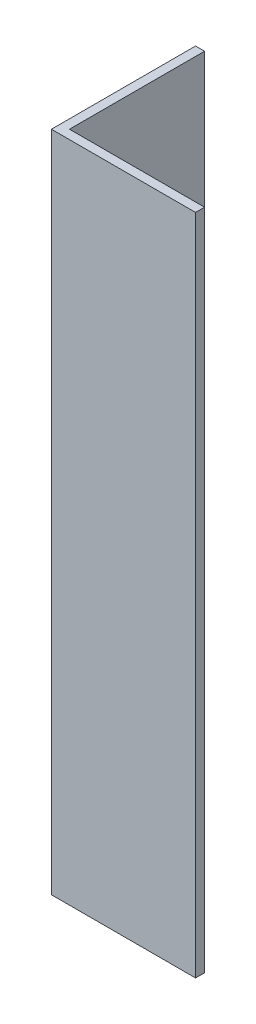
SolidWorks part; units mm, degrees
ref_plane "Front Plane" through (0, 0, 0) normal (0, 0, 1) x (1, 0, 0)
ref_plane "Top Plane" through (0, 0, 0) normal (0, 1, 0) x (1, 0, 0)
ref_plane "Right Plane" through (0, 0, 0) normal (1, 0, 0) x (0, 0, -1)
sketch "Sketch1" plane through (0, 0, 0) normal (0, 1, 0) x (1, 0, 0)
  line L0 (0, 0) -> (0, 25.4)
  line L1 (0, 25.4) -> (1.5875, 25.4)
  line L2 (1.5875, 25.4) -> (1.5875, 1.5875)
  line L3 (1.5875, 1.5875) -> (25.4, 1.5875)
  line L4 (25.4, 1.5875) -> (25.4, 0)
  line L5 (25.4, 0) -> (0, 0)
  dimension "D1" = 1.5875
  dimension "D2" = 25.4
extrude "Boss-Extrude1" add sketch "Sketch1" along normal blind 116.84
